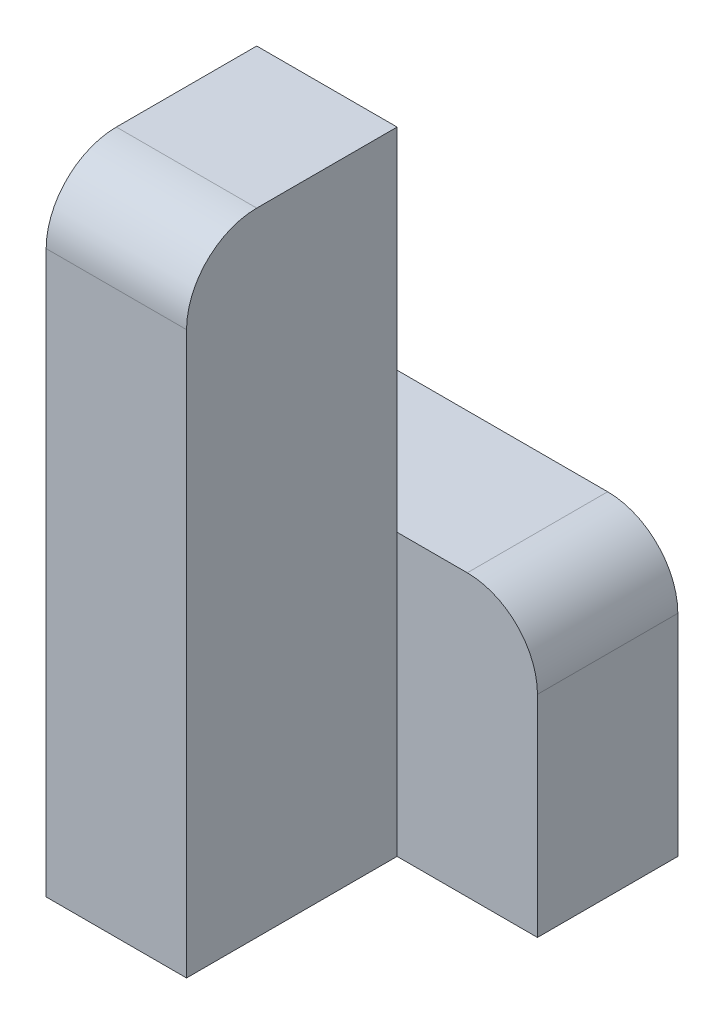
SolidWorks part; units mm, degrees
ref_plane "Front Plane" through (0, 0, 0) normal (0, 0, 1) x (1, 0, 0)
ref_plane "Top Plane" through (0, 0, 0) normal (0, 1, 0) x (1, 0, 0)
ref_plane "Right Plane" through (0, 0, 0) normal (1, 0, 0) x (0, 0, -1)
sketch "Sketch1" plane through (0, 0, 0) normal (0, 0, 1) x (1, 0, 0)
  line L1 (-30, -90) -> (-10, -90)
  line L2 (-10, -90) -> (-10, 0)
  line L3 (-10, 0) -> (-30, 0)
  line L4 (-30, 0) -> (-30, -90)
  dimension "D1" = 20
  dimension "Width" = 90
extrude "Boss-Extrude1" add sketch "Sketch1" along normal blind 30
sketch "Sketch2" plane through (0, 0, 0) normal (0, 0, 1) x (1, 0, 0)
  line L1 (-30, -90) -> (10, -90)
  line L2 (10, -90) -> (10, -50)
  line L3 (10, -50) -> (-30, -50)
  line L4 (-30, -50) -> (-30, -90)
  dimension "D1" = 40
  dimension "Width" = 40
extrude "Boss-Extrude2" add sketch "Sketch2" against normal blind 20
fillet "Fillet1" radius 10 2 edges at (10, -50, -10) (-20, 0, 30)
